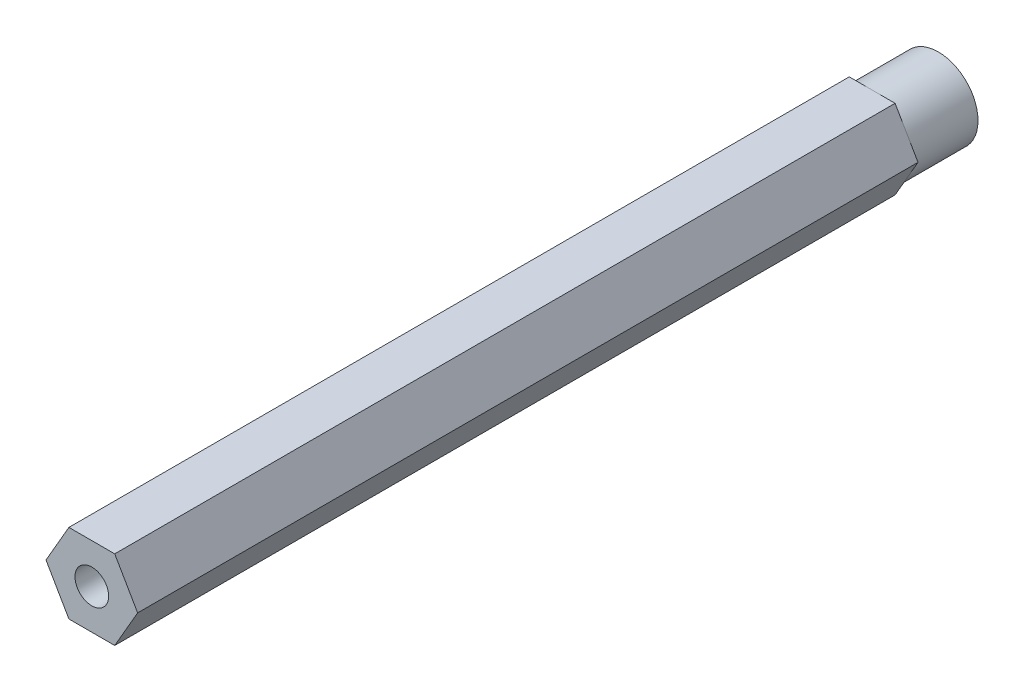
SolidWorks part; units mm, degrees
ref_plane "Front Plane" through (0, 0, 0) normal (0, 0, 1) x (1, 0, 0)
ref_plane "Top Plane" through (0, 0, 0) normal (0, 1, 0) x (1, 0, 0)
ref_plane "Right Plane" through (0, 0, 0) normal (1, 0, 0) x (0, 0, -1)
sketch "Sketch1" plane through (0, 0, 0) normal (0, 0, 1) x (1, 0, 0)
  line L1 (2.7496, -4.7625) -> (5.4993, 0)
  line L2 (5.4993, 0) -> (2.7496, 4.7625)
  line L3 (2.7496, 4.7625) -> (-2.7496, 4.7625)
  line L4 (-2.7496, 4.7625) -> (-5.4993, 0)
  line L5 (-5.4993, 0) -> (-2.7496, -4.7625)
  line L6 (-2.7496, -4.7625) -> (2.7496, -4.7625)
  circle A0 centre (0, 0) radius 4.7625 construction
  dimension "D1" = 9.525
extrude "Boss-Extrude1" add sketch "Sketch1" along normal blind 101.6
hole_wizard "#10-32 Tapped Hole1" positions "Sketch2" profile "Sketch4" tap size "#10-32" standard "ANSI Inch" end condition through all
sketch "Sketch2" plane through (0, 0, 101.6) normal (0, 0, 1) x (1, 0, 0)
  point P0 (0, 0)
sketch "Sketch4" plane through (0, 0, 101.6) normal (1, 0, 0) x (0, -1, 0)
  line L0 (0, 0) -> (0, 101.6)
  line L1 (0, 101.6) -> (2.0193, 101.6)
  line L2 (2.0193, 101.6) -> (2.0193, 0)
  line L5 (2.0193, 0) -> (0, 0)
  line L11 (0, -6.35) -> (0, 107.95) construction
  dimension "Thru Tap Drill Dia." = 4.0386
  dimension "Thru Tap Drill Depth" = 101.6
cosmetic thread "Hole Thread1" parameters "D2"=4.826
sketch "Sketch5" plane through (0, 0, 0) normal (0, 0, -1) x (-1, 0, 0)
  circle A0 centre (0, 0) radius 4.7625
  dimension "D1" = 9.525
extrude "Cut-Extrude1" cut sketch "Sketch5" against normal blind 7.9375 flip side to cut
